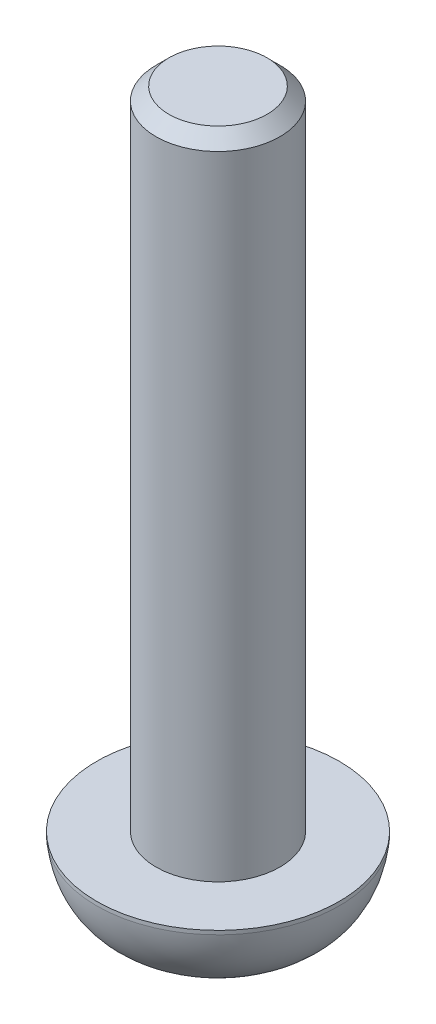
SolidWorks part; units mm, degrees
ref_plane "Front Plane" through (0, 0, 0) normal (0, 0, 1) x (1, 0, 0)
ref_plane "Top Plane" through (0, 0, 0) normal (0, 1, 0) x (1, 0, 0)
ref_plane "Right Plane" through (0, 0, 0) normal (1, 0, 0) x (0, 0, -1)
sketch "Sketch1" plane through (0, 0, 0) normal (0, 1, 0) x (1, 0, 0)
  circle A0 centre (0, 0) radius 4.7
  dimension "D1" = 9.4
extrude "Boss-Extrude1" add sketch "Sketch1" along normal blind 3
sketch "Sketch2" plane through (0, 3, 0) normal (0, 1, 0) x (1, 0, 0)
  circle A0 centre (0, 0) radius 2.4
  dimension "D1" = 4.8
extrude "Boss-Extrude2" add sketch "Sketch2" along normal blind 25
sketch "Sketch3" plane through (0, 0, 0) normal (0, 0, 1) x (1, 0, 0)
  line L0 (0, 0) -> (0, 3) construction
  line L1 (4.7, 3) -> (-4.7, 3) construction
  line L3 (-4.7, 0) -> (4.7, 0) construction
  line L4 (4.7, 0) -> (4.7, 3) construction
  line L5 (2.35, 0) -> (4.7, 0)
  line L6 (4.7, 0) -> (4.7, 2.85)
  spline S0 degree 2 poles (2.35, 0) (4.4325, 0.5996) (4.7, 2.85) knots 0 0 0 1 1 1
  dimension "D1" = 4.7
  dimension "D2" = 0.15
revolve "Cut-Revolve1" cut sketch "Sketch3" angle 360 about L0
sketch "Sketch4" plane through (0, 0, 0) normal (0, -1, 0) x (1, 0, 0)
  line L1 (0, 1.7321) -> (-1.5, 0.866)
  line L2 (-1.5, 0.866) -> (-1.5, -0.866)
  line L3 (-1.5, -0.866) -> (0, -1.7321)
  line L4 (0, -1.7321) -> (1.5, -0.866)
  line L5 (1.5, -0.866) -> (1.5, 0.866)
  line L6 (1.5, 0.866) -> (0, 1.7321)
  circle A0 centre (0, 0) radius 1.5 construction
  dimension "D1" = 3
extrude "Cut-Extrude1" cut sketch "Sketch4" against normal blind 1.5
chamfer "Chamfer1" distance 0.5 angle 45 1 edges at (0, 28, 2.4)
